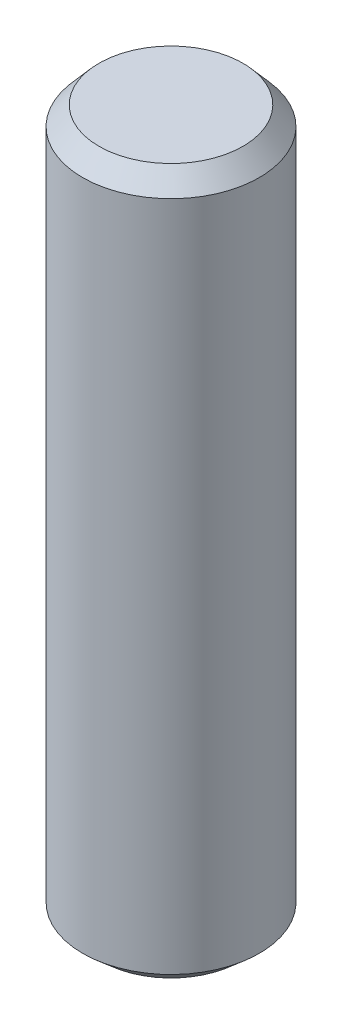
SolidWorks part; units mm, degrees
ref_plane "Front Plane" through (0, 0, 0) normal (0, 0, 1) x (1, 0, 0)
ref_plane "Top Plane" through (0, 0, 0) normal (0, 1, 0) x (1, 0, 0)
ref_plane "Right Plane" through (0, 0, 0) normal (1, 0, 0) x (0, 0, -1)
sketch "Sketch1" plane through (0, 0, 0) normal (0, 1, 0) x (1, 0, 0)
  circle A0 centre (0, 0) radius 4.7625
  dimension "D1" = 9.525
extrude "Boss-Extrude1" add sketch "Sketch1" along normal mid plane 38.1
chamfer "Chamfer1" distance 1.016 angle 41 2 edges at (0, -19.05, 4.7625) (0, 19.05, 4.7625)
